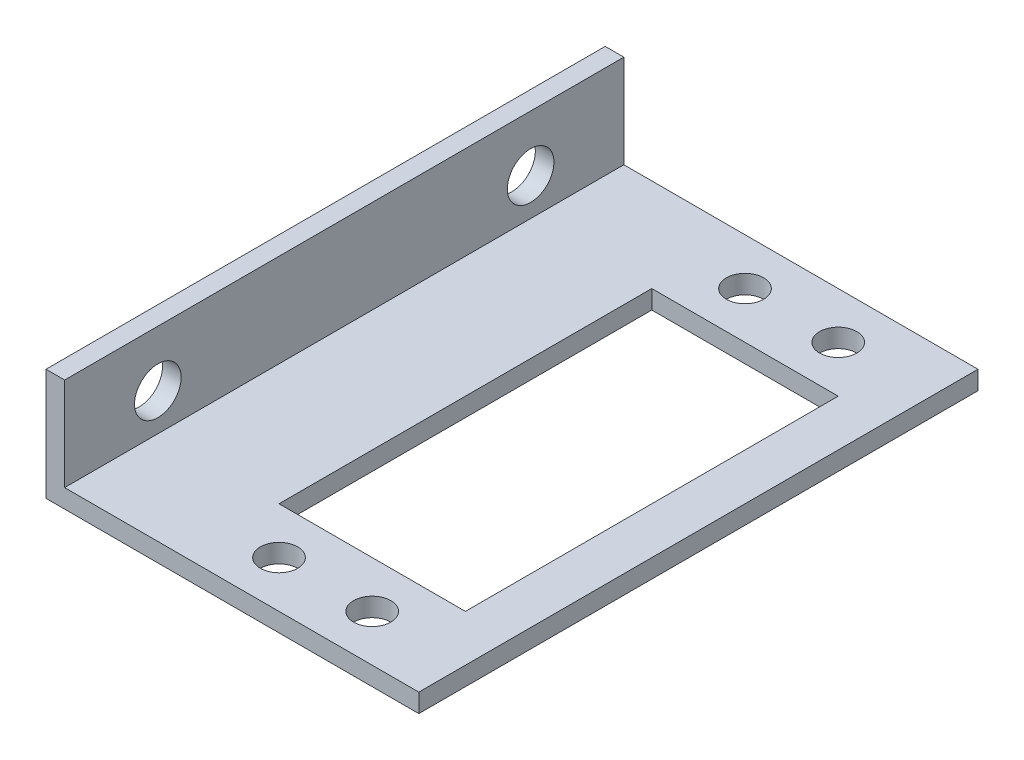
SolidWorks part; units mm, degrees
ref_plane "Alzado" through (0, 0, 0) normal (0, 0, 1) x (1, 0, 0)
ref_plane "Planta" through (0, 0, 0) normal (0, 1, 0) x (1, 0, 0)
ref_plane "Vista lateral" through (0, 0, 0) normal (1, 0, 0) x (0, 0, -1)
sketch "Croquis2" plane through (0, 0, 0) normal (0, 0, 1) x (1, 0, 0)
  line L0 (-27.3869, 0) -> (12.6131, 0)
  line L1 (-27.3869, 0) -> (-27.3869, 12)
  line L2 (-27.3869, 12) -> (-25.3869, 12)
  line L3 (-25.3869, 12) -> (-25.3869, 2)
  line L4 (-25.3869, 2) -> (12.6131, 2)
  line L5 (12.6131, 2) -> (12.6131, 0)
  dimension "D1" = 12
  dimension "D2" = 40
  dimension "D3" = 2
  dimension "D4" = 2
extrude "Saliente-Extruir1" add sketch "Croquis2" along normal blind 60
sketch "Croquis3" plane through (-27.3869, 0, 0) normal (-1, 0, 0) x (0, 0, 1)
  line L0 (60, 0) -> (0, 0) construction
  circle A0 centre (10, 6) radius 2.5
  circle A1 centre (50, 6) radius 2.5
  point P6 (30, 0)
  dimension "D1" = 5
  dimension "D2" = 5
  dimension "D3" = 20
  dimension "D4" = 20
  dimension "D5" = 6
extrude "Cortar-Extruir1" cut sketch "Croquis3" against normal blind 60
sketch "Croquis4" plane through (0, 0, 0) normal (0, -1, 0) x (1, 0, 0)
  line L1 (-12.3869, 50) -> (7.6131, 50)
  line L2 (-12.3869, 50) -> (-12.3869, 10)
  line L3 (-12.3869, 10) -> (7.6131, 10)
  line L4 (7.6131, 50) -> (7.6131, 10)
  line L5 (-12.3869, 50) -> (7.6131, 10) construction
  line L6 (-12.3869, 10) -> (7.6131, 50) construction
  circle A0 centre (-7.3869, 55) radius 2
  circle A1 centre (2.6131, 55) radius 2
  circle A2 centre (-7.3869, 5) radius 2
  circle A3 centre (2.6131, 5) radius 2
  point P0 (-2.3869, 30)
  point P15 (0, 0)
  point P16 (0, 0)
  point P17 (0, 0)
  point P20 (0, 0)
  dimension "D5" = 4
  dimension "D6" = 4
  dimension "D7" = 4
  dimension "D8" = 4
  dimension "D1" = 40
  dimension "D2" = 20
  dimension "D3" = 15
  dimension "D4" = 10
  dimension "D9" = 10
  dimension "D10" = 10
  dimension "D11" = 5
  dimension "D12" = 5
  dimension "D13" = 5
extrude "Cortar-Extruir2" cut sketch "Croquis4" against normal blind 60
